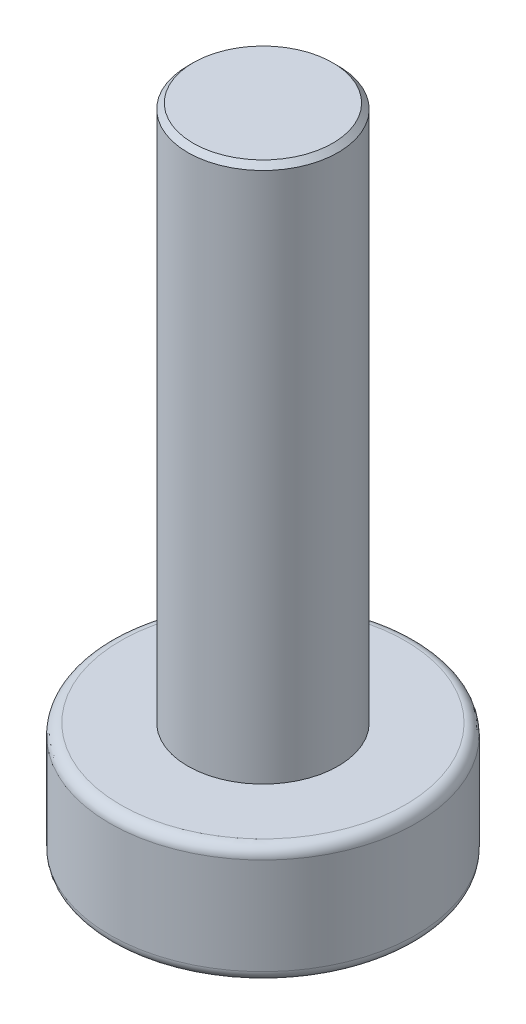
SolidWorks part; units mm, degrees
ref_plane "Спереди" through (0, 0, 0) normal (0, 0, 1) x (1, 0, 0)
ref_plane "Сверху" through (0, 0, 0) normal (0, 1, 0) x (1, 0, 0)
ref_plane "Справа" through (0, 0, 0) normal (1, 0, 0) x (0, 0, -1)
sketch "Эскиз1" plane through (0, 0, 0) normal (0, 1, 0) x (1, 0, 0)
  circle A0 centre (0, 0) radius 2.85
  dimension "D1" = 5.7
extrude "Бобышка-Вытянуть1" add sketch "Эскиз1" along normal blind 2.2
sketch "Эскиз2" plane through (0, 2.2, 0) normal (0, 1, 0) x (1, 0, 0)
  circle A0 centre (0, 0) radius 1.4
  dimension "D1" = 2.8
extrude "Бобышка-Вытянуть2" add sketch "Эскиз2" along normal blind 10
chamfer "Фаска1" distance 0.1 angle 45 1 edges at (0, 12.2, 1.4)
fillet "Скругление1" radius 0.2 2 edges at (0, 2.2, 2.85) (0, 0, 2.85)
sketch "Эскиз3" plane through (0, 0, 0) normal (0, -1, 0) x (1, 0, 0)
  line L0 (-0.5, 0.5) -> (-0.5, 2)
  line L1 (-0.5, 2) -> (0.5, 2)
  line L2 (0.5, 2) -> (0.5, 0.5)
  line L3 (0.5, 0.5) -> (2, 0.5)
  line L4 (2, 0.5) -> (2, -0.5)
  line L5 (2, -0.5) -> (0.5, -0.5)
  line L6 (0.5, -0.5) -> (0.5, -2)
  line L7 (0.5, -2) -> (-0.5, -2)
  line L8 (-0.5, -2) -> (-0.5, -0.5)
  line L9 (-0.5, -0.5) -> (-2, -0.5)
  line L10 (-2, -0.5) -> (-2, 0.5)
  line L11 (-2, 0.5) -> (-0.5, 0.5)
  point P12 (0, 2)
  point P13 (0, -2)
  point P15 (-2, 0)
  point P16 (2, 0)
  dimension "D1" = 4
  dimension "D2" = 1
extrude "Вырез-Вытянуть1" cut sketch "Эскиз3" against normal blind 1.5
